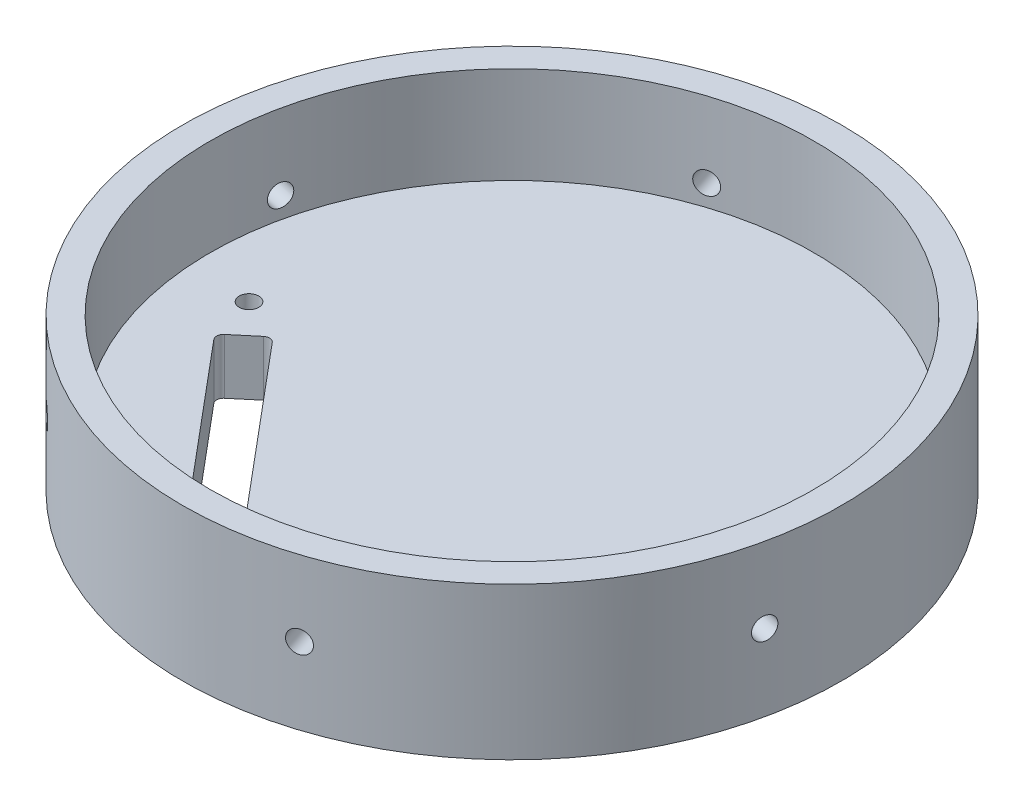
SolidWorks part; units mm, degrees
material "6061-T4 (SS)"
ref_plane "Front Plane" through (0, 0, 0) normal (0, 0, 1) x (1, 0, 0)
ref_plane "Top Plane" through (0, 0, 0) normal (0, 1, 0) x (1, 0, 0)
ref_plane "Right Plane" through (0, 0, 0) normal (1, 0, 0) x (0, 0, -1)
sketch "Sketch1" plane through (0, 0, 0) normal (0, 1, 0) x (1, 0, 0)
  circle A0 centre (0, 0) radius 75.692
  circle A1 centre (0, 0) radius 69.342
  dimension "D1" = 151.384
  dimension "D2" = 138.684
extrude "Boss-Extrude1" add sketch "Sketch1" along normal blind 22.225
sketch "Sketch2" plane through (0, 0, 0) normal (0, -1, 0) x (1, 0, 0)
  circle A0 centre (0, 0) radius 75.692
  dimension "D1" = 151.384
extrude "Boss-Extrude2" add sketch "Sketch2" along normal blind 12.7
hole_wizard "Tap Drill for 1/4-20 Tap1" positions "3DSketch2" profile "Sketch4" hole size "1/4-20" standard "ANSI Inch"
sketch3d "3DSketch2"
  line L0 (73.6526, 22.225, 17.4519) -> (73.9972, 4.8963, 15.9279)
  circle A1 centre (0, 22.225, 0) radius 75.692 construction
  point P0 (73.9972, 4.8963, 15.9279)
  point P10 (0, 97.917, 0)
  point P12 (-133.403, 50.4262, 0)
  dimension "D1" = 17.399
sketch "Sketch4" plane through (73.9972, 4.8963, 15.9279) normal (0, 1, 0) x (0.2104, 0, -0.9776)
  line L0 (0, 0) -> (0, 11.1858)
  line L1 (0, 11.1858) -> (2.5527, 9.652)
  line L2 (2.5527, 9.652) -> (2.5527, 0)
  line L5 (2.5527, 0) -> (0, 0)
  line L10 (0, 11.1858) -> (-2.5527, 9.652) construction
  line L11 (0, -6.35) -> (0, 107.95) construction
  dimension "Hole Dia." = 5.1054
  dimension "Hole Depth" = 9.652
  dimension "Drill Angle" = 118
pattern_circular "CirPattern1" count 6 over 360 about axis through (0, 22.225, 0) along (0, -1, 0) of "Tap Drill for 1/4-20 Tap1"
sketch "Sketch5" plane through (0, 0, 0) normal (0, 1, 0) x (1, 0, 0)
  line L0 (0, 0) -> (0, -69.342) construction
  line L1 (-52.6502, -15.6476) -> (-45.3536, -9.525)
  line L2 (-52.6502, -15.6476) -> (-19.9966, -54.5626)
  line L3 (-19.9966, -54.5626) -> (-12.7, -48.4401)
  line L4 (-45.3536, -9.525) -> (-12.7, -48.4401)
  circle A0 centre (0, 0) radius 69.342 construction
  dimension "D1" = 40
  dimension "D2" = 9.525
  dimension "D3" = 50.8
  dimension "D4" = 12.7
  dimension "D5" = 9.525
extrude "Cut-Extrude1" cut sketch "Sketch5" against normal through all
fillet "Fillet1" radius 1.5875 4 edges at (-19.9966, -6.35, 54.5626) (-12.7, -6.35, 48.4401) (-45.3536, -6.35, 9.525) (-52.6502, -6.35, 15.6476)
ref_plane "Plane1" through (-34.953, 0, 29.3291) normal (0.766, 0, -0.6428) x (-0.6428, 0, -0.766)
sketch "Sketch6" plane through (0, 0, 0) normal (0, 1, 0) x (1, 0, 0)
  line L0 (-30.4632, -34.6799) -> (-39.4429, -23.9782) construction
  line L1 (-46.5697, -10.5454) -> (-51.4341, -14.6271) construction
  line L2 (-46.5697, -10.5454) -> (-51.4341, -14.6271)
  line L3 (-49.0019, -12.5863) -> (-55.1244, -5.2897) construction
  point P0 (-55.1244, -5.2897)
  dimension "D1" = 9.525
hole_wizard "M4 Clearance Hole1" positions "Sketch7" profile "Sketch8" hole size "M4" standard "ANSI Metric" end condition up to next
sketch "Sketch7" plane through (0, 0, 0) normal (0, 1, 0) x (1, 0, 0)
  point P0 (-55.1244, -5.2897)
sketch "Sketch8" plane through (-55.1244, 0, 5.2897) normal (1, 0, 0) x (0, 0, 1)
  line L0 (0, 0) -> (0, 12.7)
  line L1 (0, 12.7) -> (2.25, 12.7)
  line L2 (2.25, 12.7) -> (2.25, 0)
  line L5 (2.25, 0) -> (0, 0)
  line L11 (0, -6.35) -> (0, 107.95) construction
  dimension "Thru Hole Dia." = 4.5
  dimension "Thru Hole Depth" = 12.7
